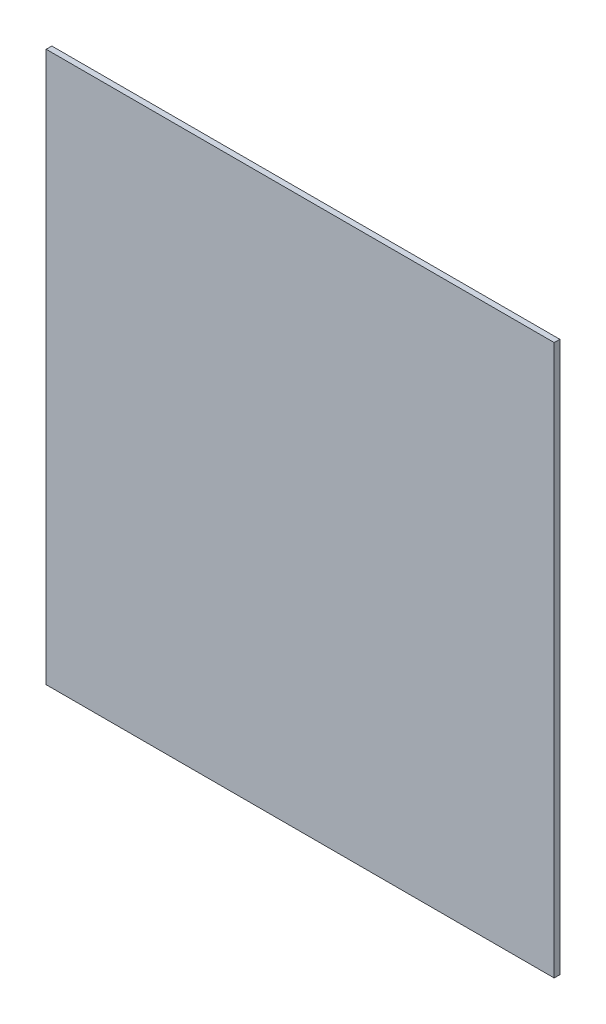
SolidWorks part; units mm, degrees
ref_plane "Front Plane" through (0, 0, 0) normal (0, 0, 1) x (1, 0, 0)
ref_plane "Top Plane" through (0, 0, 0) normal (0, 1, 0) x (1, 0, 0)
ref_plane "Right Plane" through (0, 0, 0) normal (1, 0, 0) x (0, 0, -1)
sketch "Sketch1" plane through (0, 0, 0) normal (0, 0, 1) x (1, 0, 0)
  line L1 (0, 0) -> (180, 0)
  line L2 (0, 0) -> (0, -195)
  line L3 (0, -195) -> (180, -195)
  line L4 (180, 0) -> (180, -195)
  dimension "D1" = 180
  dimension "D2" = 195
extrude "Boss-Extrude1" add sketch "Sketch1" along normal blind 2
